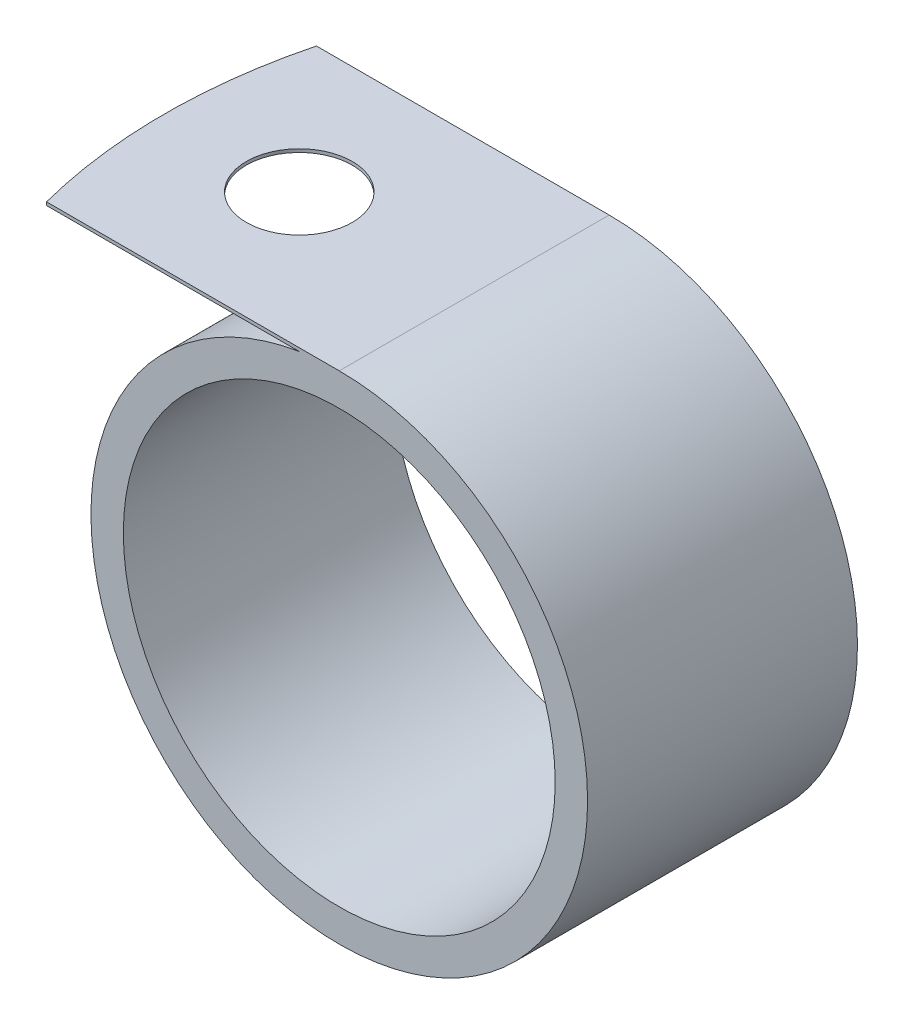
SolidWorks part; units mm, degrees
ref_plane "Front Plane" through (0, 0, 0) normal (0, 0, 1) x (1, 0, 0)
ref_plane "Top Plane" through (0, 0, 0) normal (0, 1, 0) x (1, 0, 0)
ref_plane "Right Plane" through (0, 0, 0) normal (1, 0, 0) x (0, 0, -1)
sketch "Sketch1" plane through (0, 0, 0) normal (0, 0, 1) x (1, 0, 0)
  line L0 (0, 11.684) -> (-14.581, 11.684)
  line L1 (-14.581, 11.684) -> (-14.581, 11.5316)
  line L2 (-14.581, 11.5316) -> (-1.881, 11.5316)
  circle A0 centre (0, 0) radius 10.16
  circle A1 centre (0, 0) radius 11.684
  dimension "D1" = 23.368
  dimension "D2" = 20.32
  dimension "D3" = 0.1524
  dimension "D4" = 12.7
extrude "Boss-Extrude1" add sketch "Sketch1" along normal mid plane 12.7 contours A1 A0 | A1 L0 L1 L2
sketch "Sketch5" plane through (0, 11.684, 0) normal (0, 1, 0) x (1, 0, 0)
  line L0 (0, 6.35) -> (-14.581, 6.35) construction
  line L1 (0, -6.35) -> (-14.581, -6.35) construction
  line L2 (-14.581, -6.35) -> (-14.581, 6.35) construction
  line L7 (0, 6.35) -> (-14.581, 6.35)
  line L8 (-14.581, 6.35) -> (-14.581, -6.35)
  line L9 (-14.581, -6.35) -> (0, -6.35)
  line L10 (0, -6.35) -> (0, 6.35)
  line L11 (0, 6.35) -> (-14.581, 6.35)
  line L12 (-14.581, 6.35) -> (-14.581, -6.35)
  line L13 (-14.581, -6.35) -> (0, -6.35)
  line L14 (0, -6.35) -> (0, 6.35)
  arc A0 (-13.7744, 6.35) -> (-13.7744, -6.35) centre (10.819, 0) ccw
  circle A1 centre (-8.231, 0) radius 2.4892
  line M6 (-14.581, 6.35) -> (-14.581, -6.35)
  line M7 (-14.581, -6.35) -> (0, -6.35)
  dimension "D1" = 25.4
  dimension "D2" = 4.9784
  dimension "D3" = 6.35
  dimension "D4" = 0
extrude "Cut-Extrude1" cut sketch "Sketch5" against normal up to next contours A0 L11 M6 | A0 L12 M7 | A1
